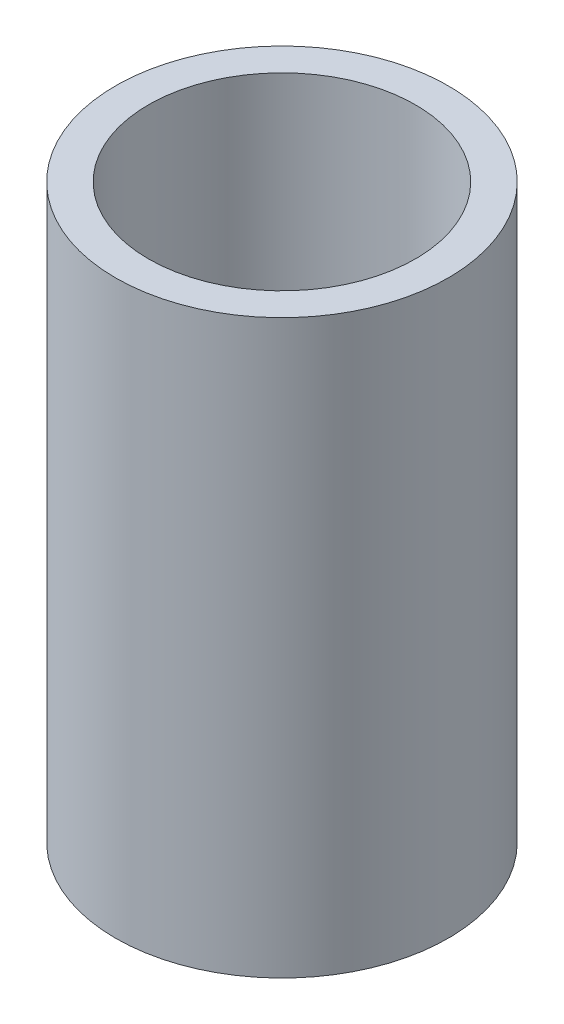
SolidWorks part; units mm, degrees
material "7075-T6 (SN)"
ref_plane "Front Plane" through (0, 0, 0) normal (0, 0, 1) x (1, 0, 0)
ref_plane "Top Plane" through (0, 0, 0) normal (0, 1, 0) x (1, 0, 0)
ref_plane "Right Plane" through (0, 0, 0) normal (1, 0, 0) x (0, 0, -1)
sketch "Sketch1" plane through (0, 0, 0) normal (0, 1, 0) x (1, 0, 0)
  circle A0 centre (0, 0) radius 12.8397
  circle A1 centre (0, 0) radius 16
  dimension "D1" = 25.6794
  dimension "D2" = 32
extrude "Boss-Extrude1" add sketch "Sketch1" along normal mid plane 55
sketch "Sketch2" plane through (0, 0, 0) normal (0, 0, 1) x (1, 0, 0)
  circle A0 centre (0, 0) radius 2
  dimension "D1" = 4
extrude "Cut-Extrude1" cut sketch "Sketch2" against normal up to next
